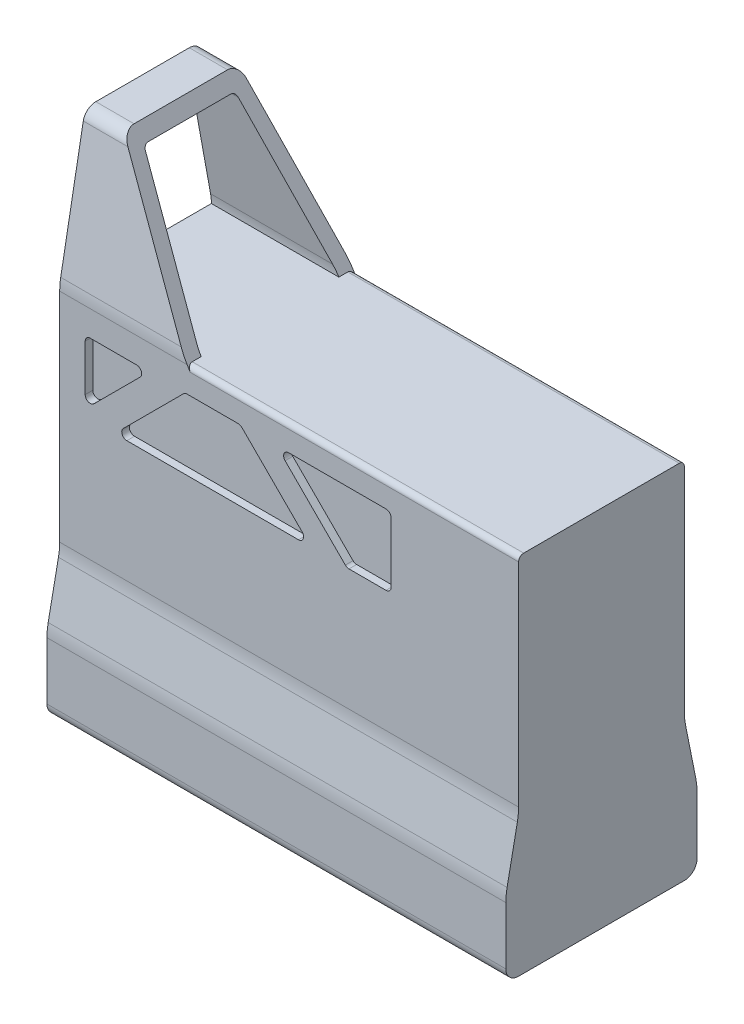
SolidWorks part; units mm, degrees
ref_plane "前视基准面" through (0, 0, 0) normal (0, 0, 1) x (1, 0, 0)
ref_plane "上视基准面" through (0, 0, 0) normal (0, 1, 0) x (1, 0, 0)
ref_plane "右视基准面" through (0, 0, 0) normal (1, 0, 0) x (0, 0, -1)
sketch "草图2" plane through (0, 0, 0) normal (1, 0, 0) x (0, 0, -1)
  line L10 (37.5, -95.1106) -> (37.5, -72.5861)
  line L11 (37.0145, -67.6832) -> (32.9855, -47.538)
  line L12 (32.5, -42.6351) -> (32.5, 42.6351)
  line L13 (32.0967, 47.1073) -> (23.2465, 95.7838)
  line L14 (18.3271, 99.8894) -> (-18.3271, 99.8894)
  line L15 (-23.2465, 95.7838) -> (-32.0967, 47.1073)
  line L16 (-32.5, 42.6351) -> (-32.5, -42.6351)
  line L17 (-32.9855, -47.538) -> (-37.0145, -67.6832)
  line L18 (-37.5, -72.5861) -> (-37.5, -95.1106)
  line L19 (-32.5, -100.1106) -> (32.5, -100.1106)
  arc A10 (37.5, -72.5861) -> (37.0145, -67.6832) centre (12.5, -72.5861) ccw
  arc A11 (32.5, -42.6351) -> (32.9855, -47.538) centre (57.5, -42.6351) ccw
  arc A12 (32.5, 42.6351) -> (32.0967, 47.1073) centre (7.5, 42.6351) ccw
  arc A13 (23.2465, 95.7838) -> (18.3271, 99.8894) centre (18.3271, 94.8894) ccw
  arc A14 (-18.3271, 99.8894) -> (-23.2465, 95.7838) centre (-18.3271, 94.8894) ccw
  arc A15 (-32.0967, 47.1073) -> (-32.5, 42.6351) centre (-7.5, 42.6351) ccw
  arc A16 (-32.9855, -47.538) -> (-32.5, -42.6351) centre (-57.5, -42.6351) ccw
  arc A17 (-37.0145, -67.6832) -> (-37.5, -72.5861) centre (-12.5, -72.5861) ccw
  arc A18 (-37.5, -95.1106) -> (-32.5, -100.1106) centre (-32.5, -95.1106) ccw
  arc A19 (32.5, -100.1106) -> (37.5, -95.1106) centre (32.5, -95.1106) ccw
extrude "凸台-拉伸2" add sketch "草图2" along normal blind 140
ref_plane "基准面2" through (15, 0, 0) normal (-1, 0, 0) x (0, 0, 1)
ref_plane "基准面3" through (50, 0, 0) normal (-1, 0, 0) x (0, 0, 1)
sketch "草图5" plane through (15, 0, 0) normal (-1, 0, 0) x (0, 0, 1)
  line L0 (-18.3271, 99.8894) -> (18.3271, 99.8894)
sketch "草图6" plane through (50, 0, 0) normal (-1, 0, 0) x (0, 0, 1)
  line L0 (-32.5, 42.6351) -> (32.5, 42.6351)
  arc A0 (-32.0967, 47.1073) -> (-32.5, 42.6351) centre (-7.5, 42.6351) ccw construction
ref_plane "基准面4" through (55.3711, 33.8488, 0) normal (0.8532, 0.5216, 0) x (0, 0, -1)
sketch "草图7" plane through (55.3711, 33.8488, 0) normal (0.8532, 0.5216, 0) x (0, 0, -1)
  line L0 (18.3271, 85.2263) -> (-18.3271, 85.2263) construction
  line L1 (-32.5, 10.298) -> (32.5, 10.298)
  line L2 (-32.5, 10.298) -> (-32.5, 85.2263)
  line L3 (-32.5, 85.2263) -> (32.5, 85.2263)
  line L4 (32.5, 10.298) -> (32.5, 85.2263)
extrude "切除-拉伸2" cut sketch "草图7" along direction (-1, 0, 0) on the side of the normal blind 150
sketch "草图8" plane through (0, 0, 0) normal (-1, 0, 0) x (0, 0, 1)
  line L6 (17.9098, 94.3894) -> (-17.9098, 94.3894)
  line L7 (-17.9098, 94.3894) -> (-26.6855, 46.1234)
  line L8 (26.6855, 46.1234) -> (17.9098, 94.3894)
  line L9 (-27, 42.6351) -> (27, 42.6351)
  arc A4 (-26.6855, 46.1234) -> (-27, 42.6351) centre (-7.5, 42.6351) ccw
  arc A5 (27, 42.6351) -> (26.6855, 46.1234) centre (7.5, 42.6351) ccw
extrude "切除-拉伸3" cut sketch "草图8" against normal blind 150
fillet "圆角1" radius 2 2 edges at (9.1811, 94.3894, 17.9098) (9.1811, 94.3894, -17.9098)
fillet "圆角2" radius 2 2 edges at (95, 42.6351, -32.5) (95, 42.6351, 32.5)
sketch "草图9" plane through (0, 0, -32.5) normal (0, 0, -1) x (-1, 0, 0)
  line L0 (0, -42.6351) -> (0, 42.6351) construction
  line L1 (-130, 32.6351) -> (-10, 32.6351)
  line L2 (-130, 32.6351) -> (-130, 5)
  line L3 (-130, 5) -> (-10, 5)
  line L4 (-10, 32.6351) -> (-10, 5)
  line L5 (-140, -42.6351) -> (-140, 40.6351) construction
  line L6 (-140, 42.6351) -> (-50, 42.6351) construction
  line L7 (-35, 32.6351) -> (-10, 7.6351)
  line L8 (-49.1421, 32.6351) -> (-21.507, 5)
  line L9 (-60, 32.6351) -> (-60, -10) construction
  line L10 (-85, 32.6351) -> (-112.6351, 5)
  line L11 (-70.8579, 32.6351) -> (-98.493, 5)
  point P21 (-110, -6.3649)
  point P22 (0, 0)
  point P23 (-115.4208, -10)
  dimension "D1" = 10
  dimension "D2" = 10
  dimension "D3" = 10
  dimension "D4" = 5
  dimension "D5" = 45
  dimension "D6" = 25
  dimension "D7" = 10
  dimension "D8" = 50
extrude "切除-拉伸4" cut sketch "草图9" against normal blind 3 contours L10 L1 L2 L3 | L9 L1 L11 L3 | L1 L9 L3 L8 | L1 L7 L4
fillet "圆角3" radius 2 11 edges at (21.507, 5, -31) (10, 7.6351, -31) (35, 32.6351, -31) (49.1421, 32.6351, -31) (10, 32.6351, -31) (70.8579, 32.6351, -31) (98.493, 5, -31) (85, 32.6351, -31) (112.6351, 5, -31) (130, 5, -31) (130, 32.6351, -31)
mirror "镜向1" about plane through (0, 0, 0) normal (0, 0, 1) of "圆角3", "切除-拉伸4"
sketch "草图10" plane through (140, 0, 0) normal (1, 0, 0) x (0, 0, -1)
  line L8 (32.5, -42.6351) -> (32.5, 40.6351)
  line L9 (30.5, 42.6351) -> (-30.5, 42.6351)
  line L10 (-32.5, 40.6351) -> (-32.5, -42.6351)
  line L11 (-32.9855, -47.538) -> (-37.0145, -67.6832)
  line L12 (-37.5, -72.5861) -> (-37.5, -95.1106)
  line L13 (-32.5, -100.1106) -> (32.5, -100.1106)
  line L14 (37.5, -95.1106) -> (37.5, -72.5861)
  line L15 (37.0145, -67.6832) -> (32.9855, -47.538)
  line L16 (32.5, -42.6351) -> (32.5, 40.6351)
  line L17 (30.5, 42.6351) -> (-30.5, 42.6351)
  line L18 (-32.5, 40.6351) -> (-32.5, -42.6351)
  line L19 (-32.9855, -47.538) -> (-37.0145, -67.6832)
  line L20 (-37.5, -72.5861) -> (-37.5, -95.1106)
  line L21 (-32.5, -100.1106) -> (32.5, -100.1106)
  line L22 (37.5, -95.1106) -> (37.5, -72.5861)
  line L23 (37.0145, -67.6832) -> (32.9855, -47.538)
  arc A8 (32.5, 40.6351) -> (30.5, 42.6351) centre (30.5, 40.6351) ccw
  arc A9 (-30.5, 42.6351) -> (-32.5, 40.6351) centre (-30.5, 40.6351) ccw
  arc A10 (-32.9855, -47.538) -> (-32.5, -42.6351) centre (-57.5, -42.6351) ccw
  arc A11 (-37.0145, -67.6832) -> (-37.5, -72.5861) centre (-12.5, -72.5861) ccw
  arc A12 (-37.5, -95.1106) -> (-32.5, -100.1106) centre (-32.5, -95.1106) ccw
  arc A13 (32.5, -100.1106) -> (37.5, -95.1106) centre (32.5, -95.1106) ccw
  arc A14 (37.5, -72.5861) -> (37.0145, -67.6832) centre (12.5, -72.5861) ccw
  arc A15 (32.5, -42.6351) -> (32.9855, -47.538) centre (57.5, -42.6351) ccw
  arc A16 (32.5, 40.6351) -> (30.5, 42.6351) centre (30.5, 40.6351) ccw
  arc A17 (-30.5, 42.6351) -> (-32.5, 40.6351) centre (-30.5, 40.6351) ccw
  arc A18 (-32.9855, -47.538) -> (-32.5, -42.6351) centre (-57.5, -42.6351) ccw
  arc A19 (-37.0145, -67.6832) -> (-37.5, -72.5861) centre (-12.5, -72.5861) ccw
  arc A20 (-37.5, -95.1106) -> (-32.5, -100.1106) centre (-32.5, -95.1106) ccw
  arc A21 (32.5, -100.1106) -> (37.5, -95.1106) centre (32.5, -95.1106) ccw
  arc A22 (37.5, -72.5861) -> (37.0145, -67.6832) centre (12.5, -72.5861) ccw
  arc A23 (32.5, -42.6351) -> (32.9855, -47.538) centre (57.5, -42.6351) ccw
  dimension "D1" = 0
extrude "凸台-拉伸3" add sketch "草图10" along normal blind 40
